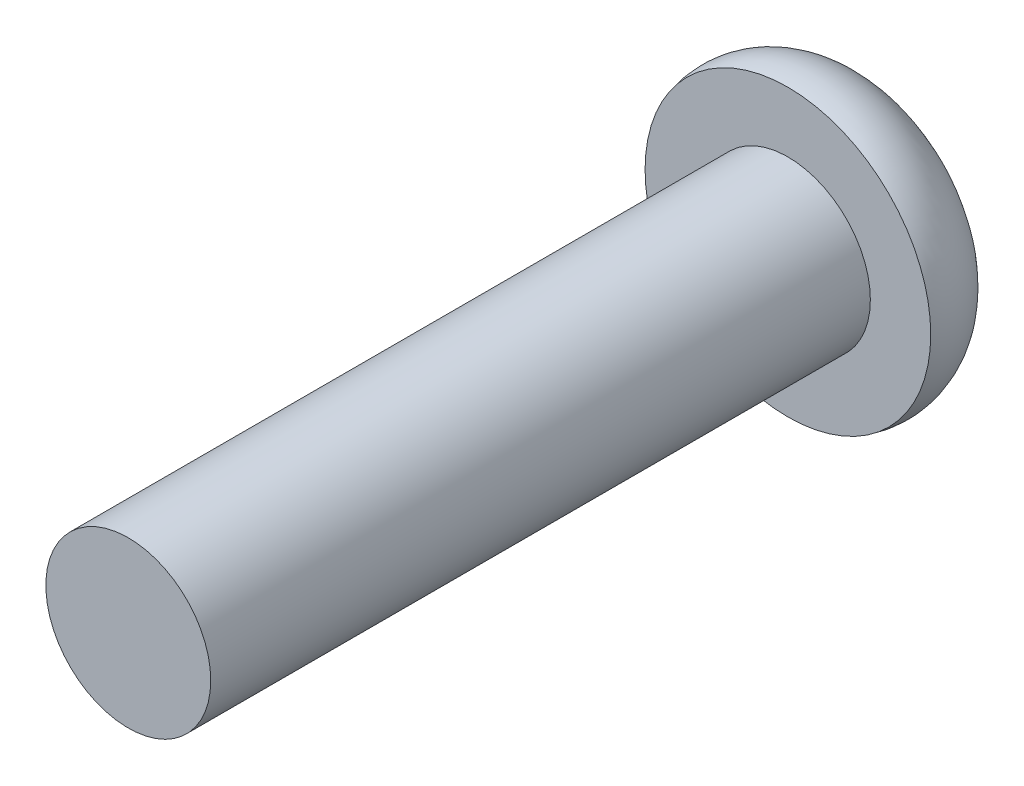
SolidWorks part; units mm, degrees
ref_plane "Front Plane" through (0, 0, 0) normal (0, 0, 1) x (1, 0, 0)
ref_plane "Top Plane" through (0, 0, 0) normal (0, 1, 0) x (1, 0, 0)
ref_plane "Right Plane" through (0, 0, 0) normal (1, 0, 0) x (0, 0, -1)
sketch "Sketch1" plane through (0, 0, 0) normal (0, 1, 0) x (1, 0, 0)
  line L0 (0, 0) -> (0, 28.65) construction
  line L1 (0, 0) -> (-3.175, 0)
  line L2 (-3.175, 0) -> (-3.175, 25.4)
  line L3 (-3.175, 25.4) -> (-5.5, 25.4)
  line L4 (-3, 28.65) -> (0, 28.65)
  line L5 (0, 0) -> (0, 28.65)
  arc A0 (-5.5, 25.4) -> (-3, 28.65) centre (-3, 26.0635) cw
  dimension "D5" = 3
  dimension "D1" = 3.175
  dimension "D2" = 5.5
  dimension "D3" = 3.25
  dimension "D4" = 25.4
revolve "Revolve1" add sketch "Sketch1" angle 360 about L0
sketch "Sketch2" plane through (0, 0, -28.65) normal (0, 0, -1) x (-1, 0, 0)
  line L1 (0, -2.3094) -> (2, -1.1547)
  line L2 (2, -1.1547) -> (2, 1.1547)
  line L3 (2, 1.1547) -> (0, 2.3094)
  line L4 (0, 2.3094) -> (-2, 1.1547)
  line L5 (-2, 1.1547) -> (-2, -1.1547)
  line L6 (-2, -1.1547) -> (0, -2.3094)
  circle A0 centre (0, 0) radius 2 construction
  dimension "D1" = 4
extrude "Cut-Extrude1" cut sketch "Sketch2" against normal blind 3.25
